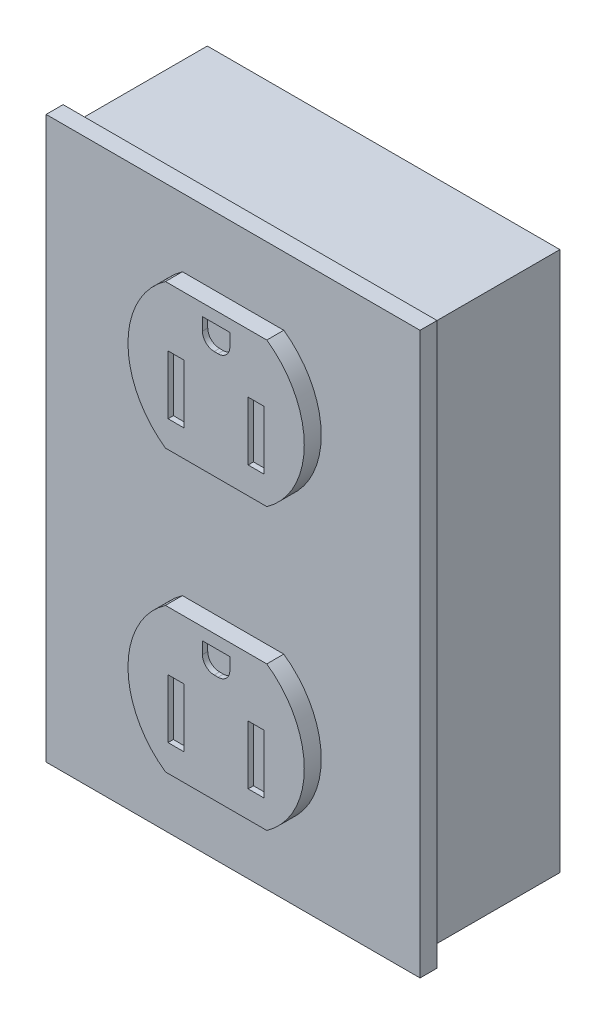
SolidWorks part; units mm, degrees
ref_plane "Alzado" through (0, 0, 0) normal (0, 0, 1) x (1, 0, 0)
ref_plane "Planta" through (0, 0, 0) normal (0, 1, 0) x (1, 0, 0)
ref_plane "Vista lateral" through (0, 0, 0) normal (1, 0, 0) x (0, 0, -1)
sketch "Croquis1" plane through (0, 0, 0) normal (0, 0, 1) x (1, 0, 0)
  line L1 (0, 0) -> (70, 0)
  line L2 (0, 0) -> (0, -105)
  line L3 (0, -105) -> (70, -105)
  line L4 (70, 0) -> (70, -105)
  dimension "D1" = 70
  dimension "D2" = 105
extrude "Saliente-Extruir1" add sketch "Croquis1" along normal blind 3.175
sketch "Croquis2" plane through (0, 0, 3.175) normal (0, 0, 1) x (1, 0, 0)
  line L0 (35, 0) -> (35, -52.5) construction
  line L1 (70, 0) -> (0, 0) construction
  line L2 (35, -52.5) -> (70, -52.5) construction
  line L3 (70, -105) -> (70, 0) construction
  circle A0 centre (35, -26.25) radius 16.5
  circle A1 centre (35, -78.75) radius 16.5
  dimension "D1" = 33
extrude "Saliente-Extruir2" add sketch "Croquis2" along normal blind 3.175
sketch "Croquis3" plane through (0, 0, 6.35) normal (0, 0, 1) x (1, 0, 0)
  line L0 (18.5, -26.25) -> (51.5, -26.25) construction
  line L1 (18.5, -78.75) -> (51.5, -78.75) construction
  line L2 (22, -45.75) -> (48, -39.75) construction
  line L3 (22, -12.75) -> (48, -12.75)
  line L4 (22, -12.75) -> (22, -6.75)
  line L5 (22, -6.75) -> (48, -6.75)
  line L6 (48, -12.75) -> (48, -6.75)
  line L7 (22, -12.75) -> (48, -6.75) construction
  line L8 (22, -6.75) -> (48, -12.75) construction
  line L9 (22, -39.75) -> (48, -45.75) construction
  line L10 (48, -39.75) -> (48, -45.75)
  line L11 (22, -45.75) -> (48, -45.75)
  line L12 (22, -39.75) -> (22, -45.75)
  line L13 (22, -39.75) -> (48, -39.75)
  line L14 (0, -52.5) -> (70, -52.5) construction
  line L15 (0, 0) -> (0, -105) construction
  line L16 (70, -105) -> (70, 0) construction
  line L17 (22, -65.25) -> (48, -59.25) construction
  line L18 (22, -98.25) -> (48, -92.25) construction
  line L19 (22, -92.25) -> (48, -98.25) construction
  line L20 (22, -59.25) -> (48, -65.25) construction
  line L21 (18.5, -78.75) -> (51.5, -78.75) construction
  line L22 (22, -65.25) -> (48, -65.25)
  line L23 (22, -65.25) -> (22, -59.25)
  line L24 (22, -59.25) -> (48, -59.25)
  line L25 (48, -65.25) -> (48, -59.25)
  line L26 (48, -92.25) -> (48, -98.25)
  line L27 (22, -98.25) -> (48, -98.25)
  line L28 (22, -92.25) -> (22, -98.25)
  line L29 (22, -92.25) -> (48, -92.25)
  circle A0 centre (35, -26.25) radius 16.5 construction
  circle A1 centre (35, -26.25) radius 16.5 construction
  circle A2 centre (35, -78.75) radius 16.5 construction
  circle A3 centre (35, -78.75) radius 16.5 construction
  point P14 (35, -9.75)
  point P23 (35, -42.75)
  point P38 (35, -62.25)
  point P39 (35, -95.25)
  dimension "D1" = 6
  dimension "D2" = 26
extrude "Cortar-Extruir1" cut sketch "Croquis3" against normal up to surface (3.175 mm away) up to face at (18.5, -78.75, 3.175)
sketch "Croquis4" plane through (0, 0, 6.35) normal (0, 0, 1) x (1, 0, 0)
  line L0 (19.1255, -21.75) -> (50.8745, -21.75) construction
  line L1 (35, -21.75) -> (35, -39.75) construction
  line L2 (25.5132, -39.75) -> (44.4868, -39.75) construction
  line L3 (25.5132, -12.75) -> (44.4868, -12.75) construction
  line L4 (26, -34.75) -> (29, -34.75)
  line L5 (26, -34.75) -> (26, -23.75)
  line L6 (26, -23.75) -> (29, -23.75)
  line L7 (29, -34.75) -> (29, -23.75)
  line L8 (26, -34.75) -> (29, -23.75) construction
  line L9 (26, -23.75) -> (29, -34.75) construction
  line L10 (44, -23.75) -> (41, -34.75) construction
  line L11 (44, -34.75) -> (41, -23.75) construction
  line L12 (41, -34.75) -> (41, -23.75)
  line L13 (44, -23.75) -> (41, -23.75)
  line L14 (44, -34.75) -> (44, -23.75)
  line L15 (44, -34.75) -> (41, -34.75)
  line L16 (35, -21.75) -> (35, -12.75) construction
  line L17 (35, -74.25) -> (35, -92.25) construction
  line L18 (34.6321, -19.5329) -> (35.3679, -19.5329)
  line L19 (32.4321, -17.3329) -> (32.4321, -14.9671)
  line L20 (32.4321, -14.9671) -> (37.5679, -14.9671)
  line L21 (37.5679, -17.3329) -> (37.5679, -14.9671)
  line L22 (32.4321, -19.5329) -> (37.5679, -14.9671) construction
  line L23 (32.4321, -14.9671) -> (37.5679, -19.5329) construction
  line L25 (25.5132, -92.25) -> (44.4868, -92.25) construction
  line L26 (19.1255, -74.25) -> (50.8745, -74.25) construction
  line L27 (44.4868, -65.25) -> (25.5132, -65.25) construction
  line L28 (41, -76.25) -> (41, -87.25)
  line L29 (26, -76.25) -> (29, -76.25)
  line L30 (26, -76.25) -> (26, -87.25)
  line L31 (26, -87.25) -> (29, -87.25)
  line L32 (29, -76.25) -> (29, -87.25)
  line L33 (44, -87.25) -> (41, -87.25)
  line L34 (44, -76.25) -> (44, -87.25)
  line L35 (44, -76.25) -> (41, -76.25)
  line L36 (35, -74.25) -> (35, -65.25) construction
  line L38 (34.6321, -71.9736) -> (35.3679, -71.9736)
  line L39 (32.4321, -69.7736) -> (32.4321, -67.5264)
  line L40 (32.4321, -67.5264) -> (37.5679, -67.5264)
  line L41 (37.5679, -69.7736) -> (37.5679, -67.5264)
  line L42 (32.4321, -71.9736) -> (37.5679, -67.5264) construction
  line L43 (32.4321, -67.5264) -> (37.5679, -71.9736) construction
  arc A0 (25.5132, -12.75) -> (25.5132, -39.75) centre (35, -26.25) ccw construction
  arc A1 (44.4868, -39.75) -> (44.4868, -12.75) centre (35, -26.25) ccw construction
  arc A2 (35.3679, -19.5329) -> (37.5679, -17.3329) centre (35.3679, -17.3329) ccw
  arc A3 (34.6321, -19.5329) -> (32.4321, -17.3329) centre (34.6321, -17.3329) cw
  arc A4 (25.5132, -65.25) -> (25.5132, -92.25) centre (35, -78.75) ccw construction
  arc A5 (44.4868, -92.25) -> (44.4868, -65.25) centre (35, -78.75) ccw construction
  arc A6 (35.3679, -71.9736) -> (37.5679, -69.7736) centre (35.3679, -69.7736) ccw
  arc A7 (34.6321, -71.9736) -> (32.4321, -69.7736) centre (34.6321, -69.7736) cw
  point P12 (27.5, -29.25)
  point P23 (42.5, -29.25)
  point P24 (35, -17.25)
  point P36 (35, -69.75)
  dimension "D6" = 2.2
  dimension "D12" = 2.2
  dimension "D1" = 11
  dimension "D2" = 3
  dimension "D3" = 6
  dimension "D4" = 4
  dimension "D5" = 9
  dimension "D7" = 9
  dimension "D8" = 2
  dimension "D9" = 6
  dimension "D10" = 11
  dimension "D11" = 3
extrude "Cortar-Extruir2" cut sketch "Croquis4" against normal blind 1
sketch "Croquis5" plane through (0, 0, 0) normal (0, 0, -1) x (-1, 0, 0)
  line L0 (-35, 0) -> (-35, -105) construction
  line L1 (-70, 0) -> (0, 0) construction
  line L2 (0, -105) -> (-70, -105) construction
  line L3 (0, 0) -> (0, -105) construction
  line L4 (-68, -103) -> (-2, -103)
  line L5 (-68, -103) -> (-68, -2)
  line L6 (-68, -2) -> (-2, -2)
  line L7 (-2, -103) -> (-2, -2)
  line L8 (-68, -103) -> (-2, -2) construction
  line L9 (-68, -2) -> (-2, -103) construction
  point P6 (-35, -52.5)
  dimension "D1" = 2
  dimension "D2" = 2
extrude "Saliente-Extruir3" add sketch "Croquis5" along normal blind 25
